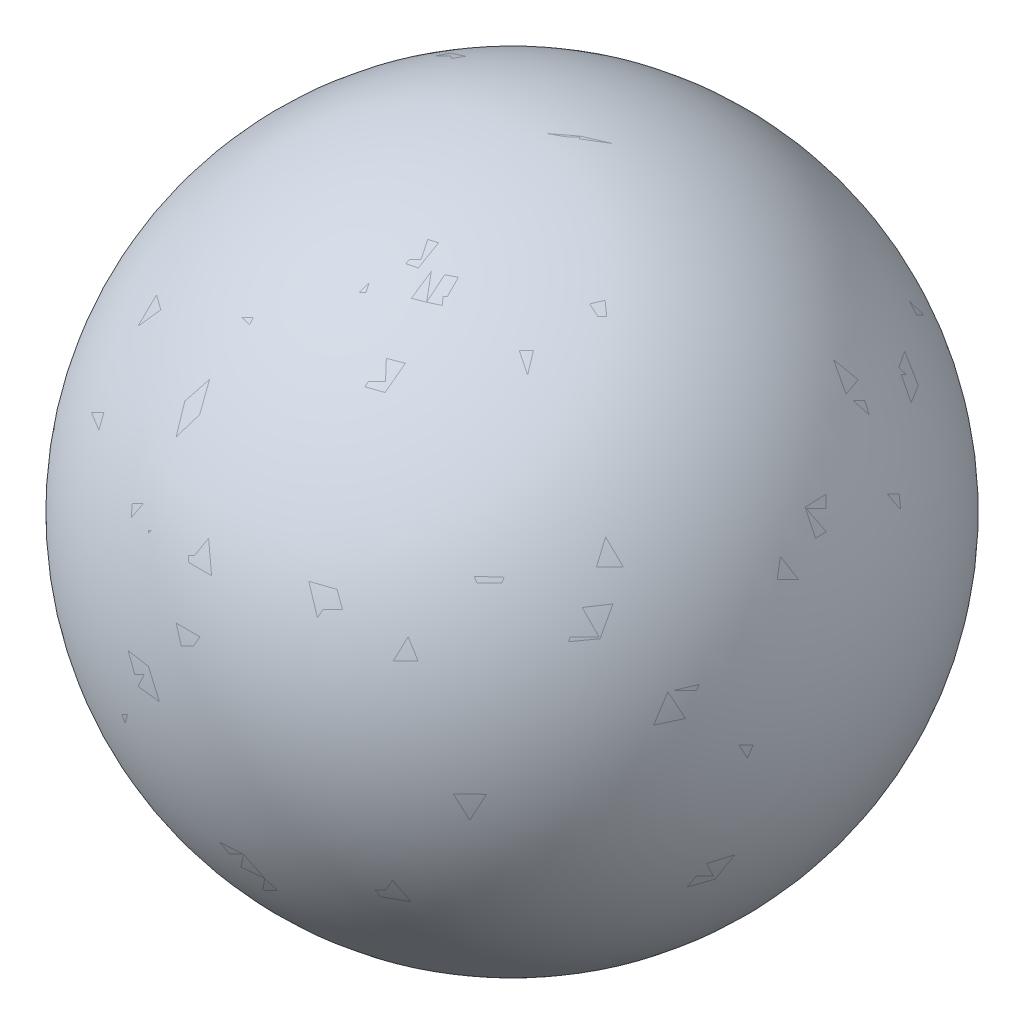
SolidWorks part; units mm, degrees
other "COLL.SPHERE-Revolve2"
ref_plane "Piano frontale" through (0, 0, 0) normal (0, 0, 1) x (1, 0, 0)
ref_plane "Piano superiore" through (0, 0, 0) normal (0, 1, 0) x (1, 0, 0)
ref_plane "Piano destro" through (0, 0, 0) normal (1, 0, 0) x (0, 0, -1)
sketch "Sketch1" plane through (0, 0, 0) normal (0, 0, 1) x (1, 0, 0)
  line L0 (0, 100) -> (0, -100)
  arc A0 (0, -100) -> (0, 100) centre (0, 0) ccw
  dimension "D1" = 200
revolve "Revolve1" add sketch "Sketch1" angle 360 about L0
sketch "Sketch2" plane through (0, 0, 0) normal (0, 0, 1) x (1, 0, 0)
  line L1 (0, 100) -> (0, -100)
  line L2 (0, 100) -> (0, -100)
  arc A1 (0, -100) -> (0, 100) centre (0, 0) ccw
  arc A2 (0, -100) -> (0, 100) centre (0, 0) ccw
  dimension "D1" = 0
revolve "Revolve2" add sketch "Sketch2" angle 360 about L2
ref_point "Point1"
